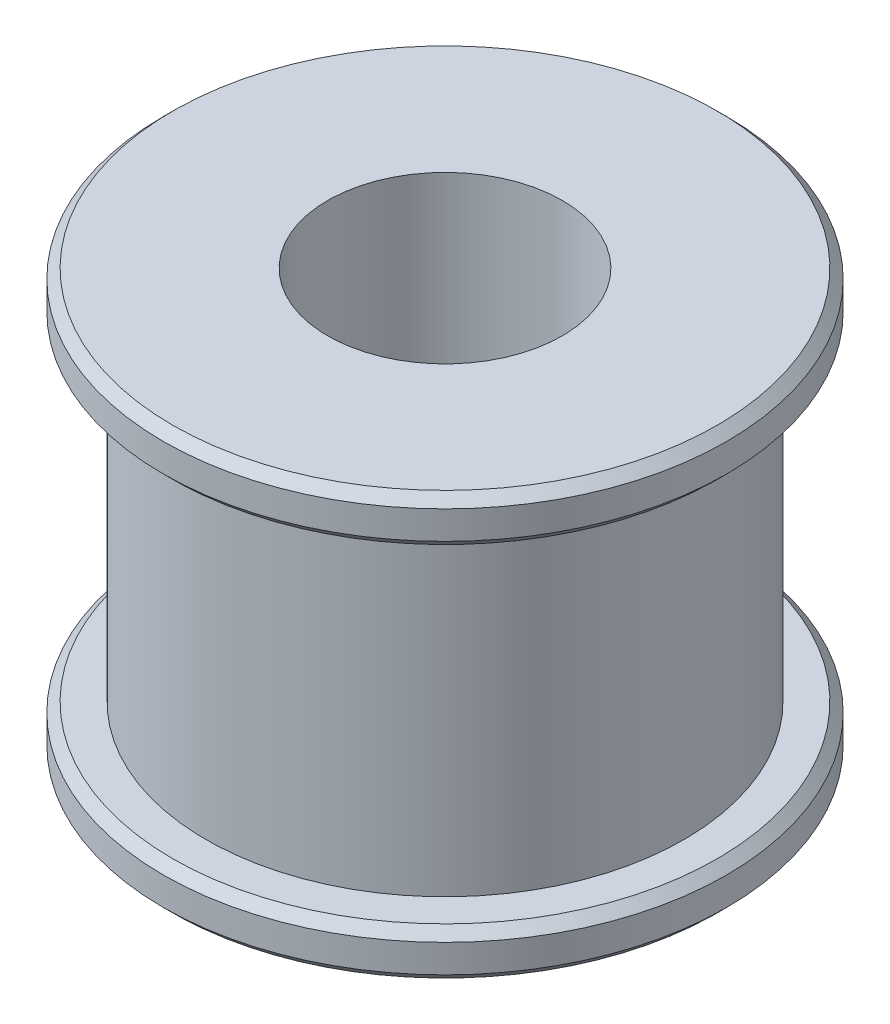
SolidWorks part; units mm, degrees
ref_plane "Front plane" through (0, 0, 0) normal (0, 0, 1) x (1, 0, 0)
ref_plane "Top plane" through (0, 0, 0) normal (0, 1, 0) x (1, 0, 0)
ref_plane "Right Plane" through (0, 0, 0) normal (1, 0, 0) x (0, 0, -1)
sketch "Sketch1" plane through (0, 0, 0) normal (0, 0, 1) x (1, 0, 0)
  line L0 (2.5, 0) -> (2.5, 9)
  line L1 (2.5, 9) -> (6, 9)
  line L2 (6, 9) -> (6, 8)
  line L3 (6, 8) -> (5.093, 8)
  line L4 (5.093, 8) -> (5.093, 1)
  line L5 (5.093, 1) -> (6, 1)
  line L6 (6, 1) -> (6, 0)
  line L7 (6, 0) -> (2.5, 0)
  line L8 (0, 0) -> (0, 9) construction
  dimension "D2" = 5
  dimension "D3" = 12
  dimension "D4" = 7
  dimension "D6" = 10.1859
  dimension "D1" = 9
revolve "Revolve1" add sketch "Sketch1" angle 360 about L8
chamfer "Chamfer1" distance 0.2 angle 45 4 edges at (0, 0, -6) (0, 1, -6) (0, 8, -6) (0, 9, -6)
equation "\"D6@Sketch1\" = 32/pi"
